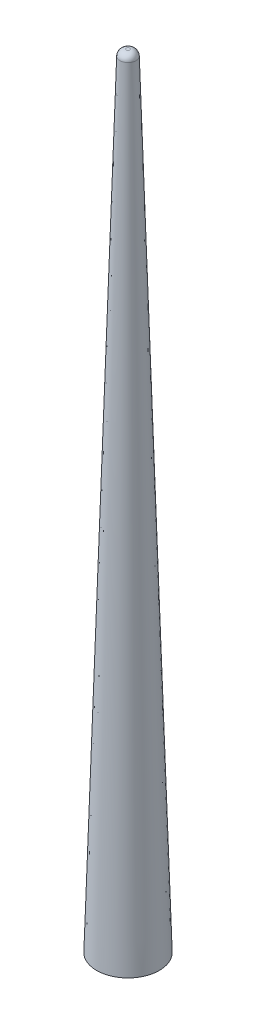
SolidWorks part; units mm, degrees
ref_plane "Front Plane" through (0, 0, 0) normal (0, 0, 1) x (1, 0, 0)
ref_plane "Top Plane" through (0, 0, 0) normal (0, 1, 0) x (1, 0, 0)
ref_plane "Right Plane" through (0, 0, 0) normal (1, 0, 0) x (0, 0, -1)
ref_plane "Plane1" through (0, 250, 0) normal (0, 1, 0) x (1, 0, 0)
sketch "Sketch1" plane through (0, 250, 0) normal (0, 1, 0) x (1, 0, 0)
  circle A0 centre (0, 0) radius 2.5
  dimension "D1" = 5
sketch "Sketch2" plane through (0, 0, 0) normal (0, 1, 0) x (1, 0, 0)
  circle A0 centre (0, 0) radius 10
  dimension "D1" = 20
loft "Loft1" add profiles "Sketch2", "Sketch1"
fillet "Fillet1" radius 2 1 edges at (0, 250, 2.5)
